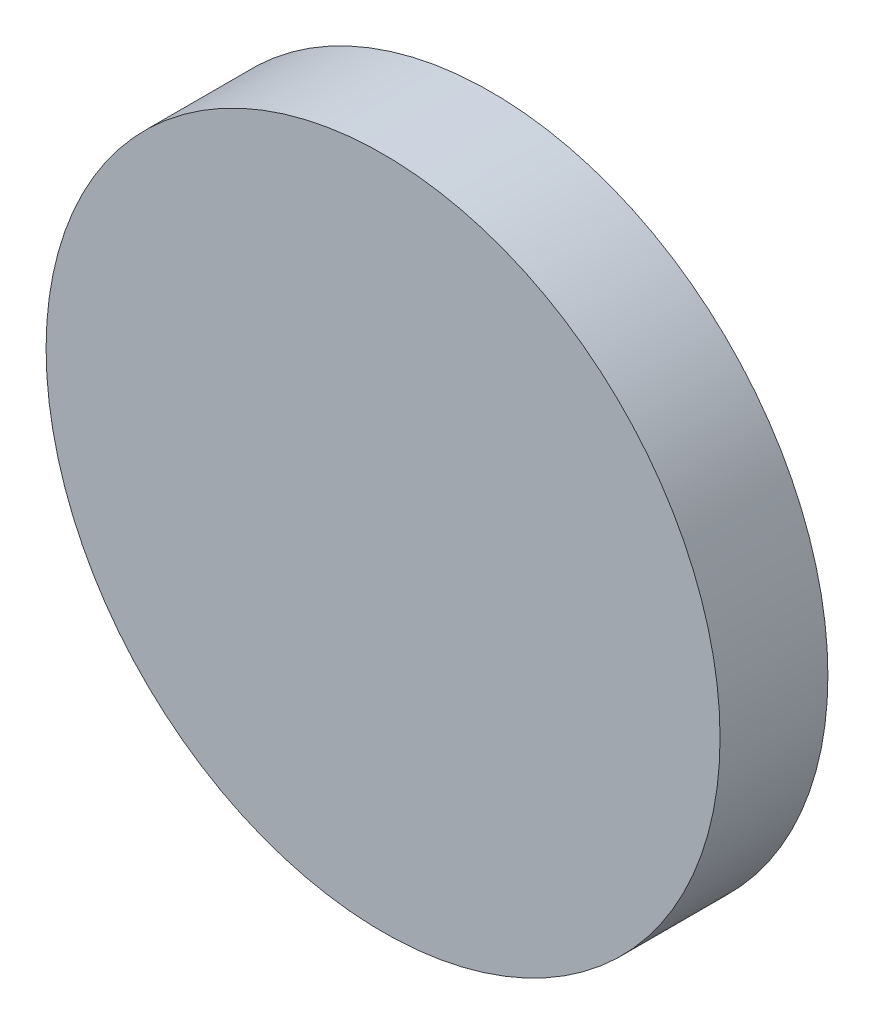
SolidWorks part; units mm, degrees
ref_plane "前视基准面" through (0, 0, 0) normal (0, 0, 1) x (1, 0, 0)
ref_plane "上视基准面" through (0, 0, 0) normal (0, 1, 0) x (1, 0, 0)
ref_plane "右视基准面" through (0, 0, 0) normal (1, 0, 0) x (0, 0, -1)
sketch "草图1" plane through (0, 0, 0) normal (0, 0, 1) x (1, 0, 0)
  circle A0 centre (0, 0) radius 6.25
  dimension "D1" = 12.5
extrude "凸台-拉伸1" add sketch "草图1" along normal blind 2
